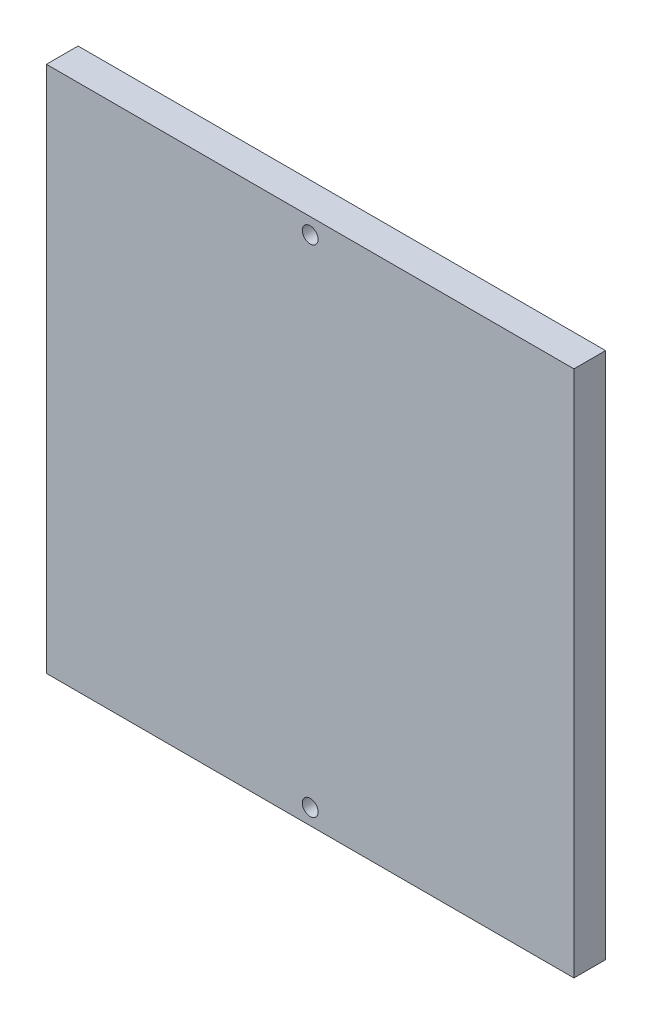
SolidWorks part; units mm, degrees
ref_plane "Front Plane" through (0, 0, 0) normal (0, 0, 1) x (1, 0, 0)
ref_plane "Top Plane" through (0, 0, 0) normal (0, 1, 0) x (1, 0, 0)
ref_plane "Right Plane" through (0, 0, 0) normal (1, 0, 0) x (0, 0, -1)
sketch "Sketch1" plane through (0, 0, 0) normal (0, 0, 1) x (1, 0, 0)
  line L0 (0, -38.3889) -> (100, -38.3889)
  line L1 (100, -38.3889) -> (100, -138.3889)
  line L2 (100, -138.3889) -> (0, -138.3889)
  line L3 (0, -138.3889) -> (0, -38.3889)
  line L4 (50, -38.3889) -> (50, -44.3889) construction
  line L5 (51.5, -44.3889) -> (48.5, -44.3889) construction
  line L6 (50, -132.3889) -> (50, -138.3889) construction
  line L7 (51.5, -132.3889) -> (48.5, -132.3889) construction
  circle A0 centre (50, -41.3889) radius 1.5
  circle A1 centre (50, -135.3889) radius 1.5
extrude "Boss-Extrude1" add sketch "Sketch1" along normal blind 6
